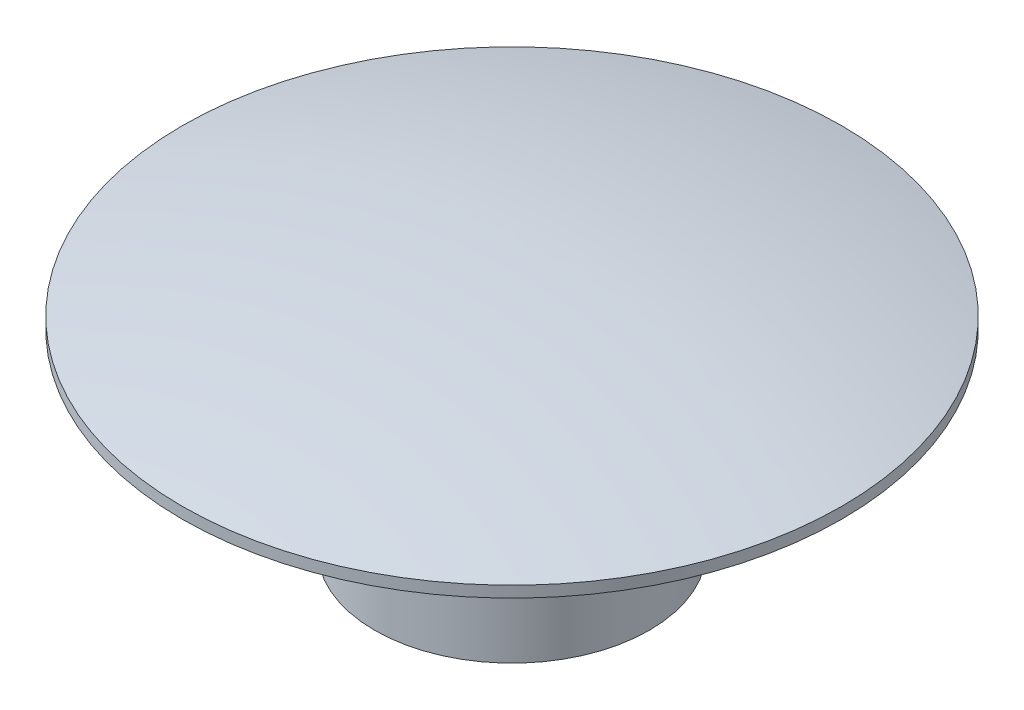
SolidWorks part; units mm, degrees
ref_plane "Plan de face" through (0, 0, 0) normal (0, 0, 1) x (1, 0, 0)
ref_plane "Plan de dessus" through (0, 0, 0) normal (0, 1, 0) x (1, 0, 0)
ref_plane "Plan de droite" through (0, 0, 0) normal (1, 0, 0) x (0, 0, -1)
sketch "Esquisse1" plane through (0, 0, 0) normal (0, 0, 1) x (1, 0, 0)
  line L0 (0, -17.3253) -> (0, 8.002) construction
  line L1 (0, 1) -> (0, -3.5)
  line L2 (0, -3.5) -> (-2.5, -3.5)
  line L3 (-2.5, -3.5) -> (-2.5, 0)
  line L4 (-2.5, 0) -> (-6, 0)
  line L5 (-6, 0) -> (-6, 0.2036)
  arc A0 (-6, 0.2036) -> (0, 1) centre (0, -22) cw
  dimension "D5" = 23
  dimension "D1" = 5
  dimension "D2" = 4.5
  dimension "D3" = 12
  dimension "D4" = 1
revolve "Révolution1" add sketch "Esquisse1" angle 360 about L0
